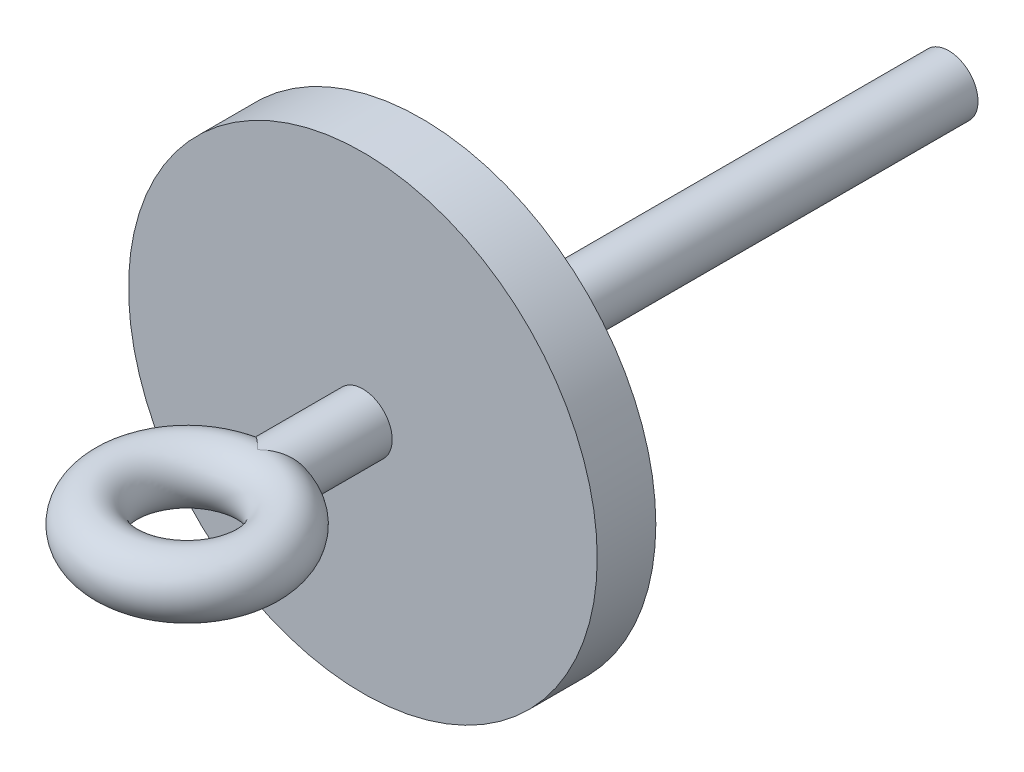
SolidWorks part; units mm, degrees
ref_plane "Front Plane" through (0, 0, 0) normal (0, 0, 1) x (1, 0, 0)
ref_plane "Top Plane" through (0, 0, 0) normal (0, 1, 0) x (1, 0, 0)
ref_plane "Right Plane" through (0, 0, 0) normal (1, 0, 0) x (0, 0, -1)
sketch "Sketch1" plane through (0, 0, 0) normal (0, 0, 1) x (1, 0, 0)
  circle A0 centre (0, 0) radius 50.8
  dimension "D1" = 101.6
extrude "Boss-Extrude1" add sketch "Sketch1" along normal blind 12.7
sketch "Sketch2" plane through (0, 0, 0) normal (0, 0, -1) x (-1, 0, 0)
  circle A0 centre (0, 0) radius 6.35
  dimension "D1" = 12.7
extrude "Boss-Extrude2" add sketch "Sketch2" along normal blind 114.3 and the other way blind 35.56
sketch "Sketch3" plane through (0, 0, 0) normal (0, 1, 0) x (1, 0, 0)
  arc A0 (0, -66.04) -> (0, -35.56) centre (0, -50.8) ccw
  dimension "D1" = 15.24
  dimension "D2" = 50.8
ref_plane "Plane1" through (0, 0, 50.8) normal (0, 0, 1) x (1, 0, 0)
sketch "Sketch4" plane through (0, 0, 50.8) normal (0, 0, 1) x (1, 0, 0)
  circle A0 centre (15.2987, 0) radius 6.35
  dimension "D1" = 12.7
sweep "Sweep3" add profiles "Sketch4" path "Sketch3"
mirror "Mirror1" about plane through (0, 0, 66.0987) normal (-1, 0, 0) of "Sweep3"
